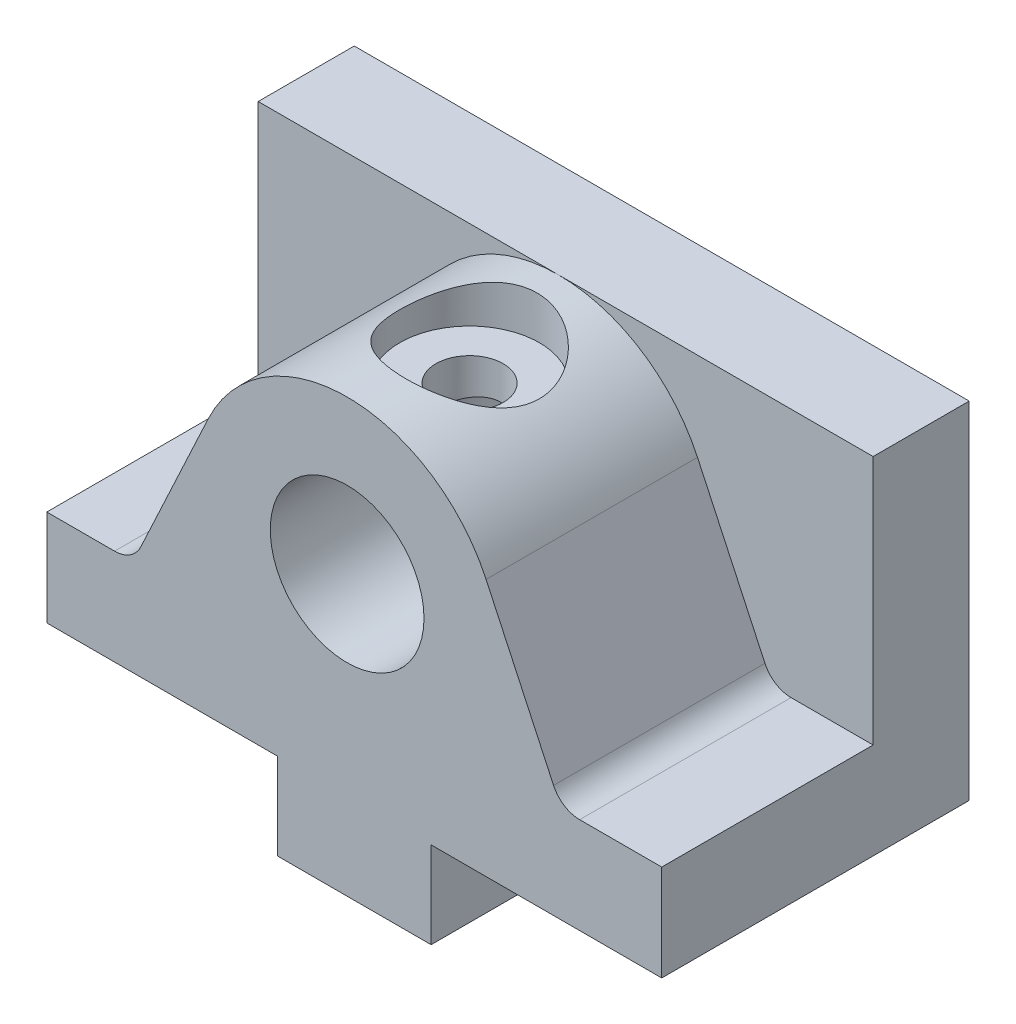
SolidWorks part; units mm, degrees
ref_plane "Front Plane" through (0, 0, 0) normal (0, 0, 1) x (1, 0, 0)
ref_plane "Top Plane" through (0, 0, 0) normal (0, 1, 0) x (1, 0, 0)
ref_plane "Right Plane" through (0, 0, 0) normal (1, 0, 0) x (0, 0, -1)
sketch "Sketch1" plane through (0, 0, 0) normal (0, 1, 0) x (1, 0, 0)
  line L1 (32, -16) -> (-32, -16)
  line L2 (32, -16) -> (32, 16)
  line L3 (32, 16) -> (-32, 16)
  line L4 (-32, -16) -> (-32, 16)
  line L5 (32, -16) -> (-32, 16) construction
  line L6 (32, 16) -> (-32, -16) construction
  point P0 (0, 0)
  dimension "D1" = 32
  dimension "D2" = 64
extrude "Boss-Extrude1" add sketch "Sketch1" along normal blind 10
sketch "Sketch4" plane through (0, 10, 0) normal (0, 1, 0) x (1, 0, 0)
  line L0 (-32, 16) -> (-32, 6)
  line L1 (-32, 16) -> (-32, -16) construction
  line L2 (-32, 6) -> (32, 6)
  line L3 (32, -16) -> (32, 16) construction
  line L4 (32, 6) -> (32, 16)
  line L5 (32, 16) -> (-32, 16)
  dimension "D1" = 10
extrude "Boss-Extrude3" add sketch "Sketch4" along normal blind 26
sketch "Sketch5" plane through (0, 0, -6) normal (0, 0, 1) x (1, 0, 0)
  line L0 (-32, 36) -> (32, 36) construction
  line L1 (-15.2047, 26.7862) -> (-23.0322, 10)
  line L2 (-32, 10) -> (32, 10) construction
  line L3 (13.7209, 26.7862) -> (21.5484, 10)
  line L4 (-32, 10) -> (32, 10) construction
  line L5 (-23.0322, 10) -> (21.5484, 10)
  arc A0 (13.7209, 26.7862) -> (-15.2047, 26.7862) centre (-0.7419, 20.0421) ccw
  dimension "D1" = 50
extrude "Boss-Extrude4" add sketch "Sketch5" along normal up to surface (22 mm away) up to face at (0, 5, 16)
fillet "Fillet1" radius 3 2 edges at (-23.0322, 10, 5) (21.5484, 10, 5)
sketch "Sketch6" plane through (0, 0, 16) normal (0, 0, 1) x (1, 0, 0)
  line L0 (-8, 0) -> (-8, -9)
  line L1 (-32, 0) -> (32, 0) construction
  line L2 (-8, -9) -> (8, -9)
  line L3 (8, -9) -> (8, 0)
  line L4 (8, 0) -> (-8, 0)
  line L5 (32, 10) -> (32, 0) construction
  dimension "D1" = 9
  dimension "D2" = 16
  dimension "D3" = 24
extrude "Boss-Extrude5" add sketch "Sketch6" against normal up to surface (32 mm away) up to face at (0, 18, -16)
sketch "Sketch7" plane through (0, 36, 0) normal (0, 1, 0) x (1, 0, 0)
  line L0 (0, 16) -> (0, -16) construction
  line L1 (32, 16) -> (-32, 16) construction
  line L2 (-15.2047, -16) -> (13.7209, -16) construction
  line L3 (-32, -4) -> (32, -4) construction
  line L4 (-32, 6) -> (-32, -16) construction
  line L5 (32, -16) -> (32, 6) construction
  dimension "D1" = 20
ref_plane "Plane1" through (0, 36, 0) normal (0, 1, 0) x (1, 0, 0)
hole_wizard "CBORE for M6 Hex Head Bolt1" positions "Sketch10" profile "Sketch11" counterbore size "M6" standard "ANSI Metric"
sketch "Sketch10" plane through (0, 36, 0) normal (0, 1, 0) x (1, 0, 0)
  line L0 (-32, -4) -> (32, -4) construction
  point P0 (0, -4)
sketch "Sketch11" plane through (0, 36, 4) normal (1, 0, 0) x (0, 0, 1)
  line L0 (0, 0) -> (0, 17.103)
  line L1 (0, 17.103) -> (3.5, 15)
  line L2 (3.5, 15) -> (3.5, 4.38)
  line L3 (3.5, 4.38) -> (7.275, 4.38)
  line L4 (7.275, 4.38) -> (7.275, 0)
  line L5 (7.275, 0) -> (0, 0)
  line L10 (0, 17.103) -> (-3.5, 15) construction
  line L11 (0, -6.35) -> (0, 107.95) construction
  dimension "Hole Dia." = 7
  dimension "Hole Depth" = 15
  dimension "C'Bore Dia." = 14.55
  dimension "C'Bore Depth" = 4.38
  dimension "Drill Angle" = 118
sketch "Sketch12" plane through (0, 0, 16) normal (0, 0, 1) x (1, 0, 0)
  circle A0 centre (-0.7419, 20.0421) radius 8
extrude "Cut-Extrude1" cut sketch "Sketch12" against normal blind 24
sketch "Sketch13" plane through (0, -9, 0) normal (0, -1, 0) x (1, 0, 0)
  line L0 (0, 16) -> (0, -16) construction
  line L1 (-8, 8) -> (8, 8) construction
  line L2 (-8, -16) -> (-8, 16) construction
  line L3 (8, -16) -> (8, 16) construction
  line L4 (-8, -8) -> (8, -8) construction
  line L5 (-8, -16) -> (-8, 16) construction
  line L6 (8, -16) -> (8, 16) construction
  line L7 (-8, 16) -> (8, 16) construction
  dimension "D1" = 8
  dimension "D2" = 16
sketch "Sketch16" plane through (0, -9, 0) normal (0, -1, 0) x (1, 0, 0)
  line L0 (-8, 8) -> (8, 8) construction
  line L1 (0, 16) -> (0, -16) construction
  line L2 (-8, 8) -> (8, 8)
  line L3 (0, 16) -> (0, -16)
hole_wizard "Tap Drill for M6x1.0 Tap1" positions "Sketch17" profile "Sketch18" hole size "M6x1.0" standard "ANSI Metric"
sketch "Sketch17" plane through (0, -9, 0) normal (0, -1, 0) x (-1, 0, 0)
  line L0 (8, 16) -> (8, -16) construction
  line L6 (-8, 16) -> (-8, -16) construction
  point P0 (0, -8)
  point P2 (0, 8)
  dimension "D1" = 8
  dimension "D2" = 16
  dimension "D3" = 8
  dimension "D4" = 8
  dimension "D5" = 8
sketch "Sketch18" plane through (0, -9, 8) normal (1, 0, 0) x (0, 0, -1)
  line L0 (0, 0) -> (0, 17.5022)
  line L1 (0, 17.5022) -> (2.5, 16)
  line L2 (2.5, 16) -> (2.5, 0)
  line L5 (2.5, 0) -> (0, 0)
  line L10 (0, 17.5022) -> (-2.5, 16) construction
  line L11 (0, -6.35) -> (0, 107.95) construction
  dimension "Hole Dia." = 5
  dimension "Hole Depth" = 16
  dimension "Drill Angle" = 118
